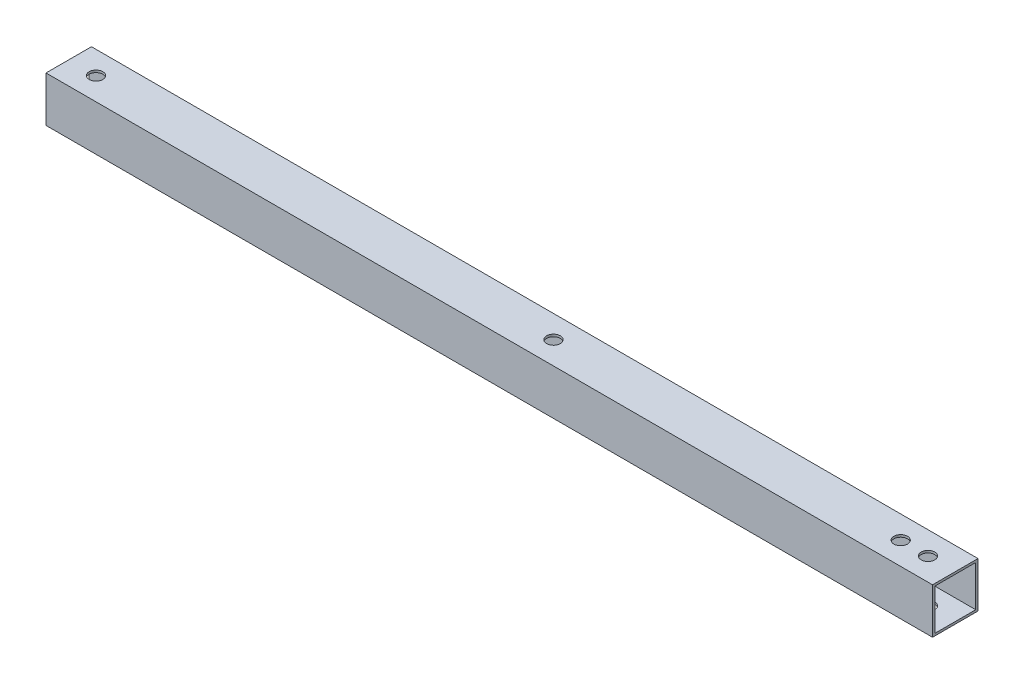
SolidWorks part; units mm, degrees
ref_plane "Front Plane" through (0, 0, 0) normal (0, 0, 1) x (1, 0, 0)
ref_plane "Top Plane" through (0, 0, 0) normal (0, 1, 0) x (1, 0, 0)
ref_plane "Right Plane" through (0, 0, 0) normal (1, 0, 0) x (0, 0, -1)
sketch "Sketch2" plane through (0, 0, 0) normal (1, 0, 0) x (0, 0, -1)
  line L0 (-9, 9) -> (9, 9)
  line L1 (-10, -10) -> (10, -10)
  line L2 (-10, -10) -> (-10, 10)
  line L3 (-10, 10) -> (10, 10)
  line L4 (10, -10) -> (10, 10)
  line L5 (-10, -10) -> (10, 10) construction
  line L6 (-10, 10) -> (10, -10) construction
  line L7 (9, -9) -> (9, 9)
  line L8 (-9, -9) -> (9, -9)
  line L9 (-9, -9) -> (-9, 9)
  point P0 (0, 0)
  dimension "D1" = 20
  dimension "D2" = 20
  dimension "D3" = 1
extrude "Boss-Extrude1" add sketch "Sketch2" along normal blind 390
sketch "Sketch3" plane through (0, 10, 0) normal (0, 1, 0) x (1, 0, 0)
  line L0 (0, 0.6451) -> (23.5, 0.6451) construction
  line L1 (0, 10) -> (0, -10) construction
  line L2 (23.5, 10) -> (23.5, -10) construction
  line L3 (390, 10) -> (0, 10) construction
  line L4 (390, -10) -> (0, -10) construction
  line L5 (201.5, 10) -> (201.5, -10) construction
  line L6 (225, 10) -> (225, -10) construction
  line L7 (201.5, 10) -> (225, -10) construction
  line L8 (225, -10) -> (201.5, -10) construction
  line L9 (201.5, -10) -> (225, 10) construction
  line L10 (195, 10) -> (195, -10) construction
  circle A0 centre (12, 0) radius 3
  circle A1 centre (213.25, 0) radius 3
  circle A2 centre (378, 0) radius 3
  circle A3 centre (366, 0) radius 3
  dimension "D1" = 12
  dimension "D4" = 6
  dimension "D2" = 178
  dimension "D3" = 23.5
extrude "Cut-Extrude1" cut sketch "Sketch3" against normal blind 1240
